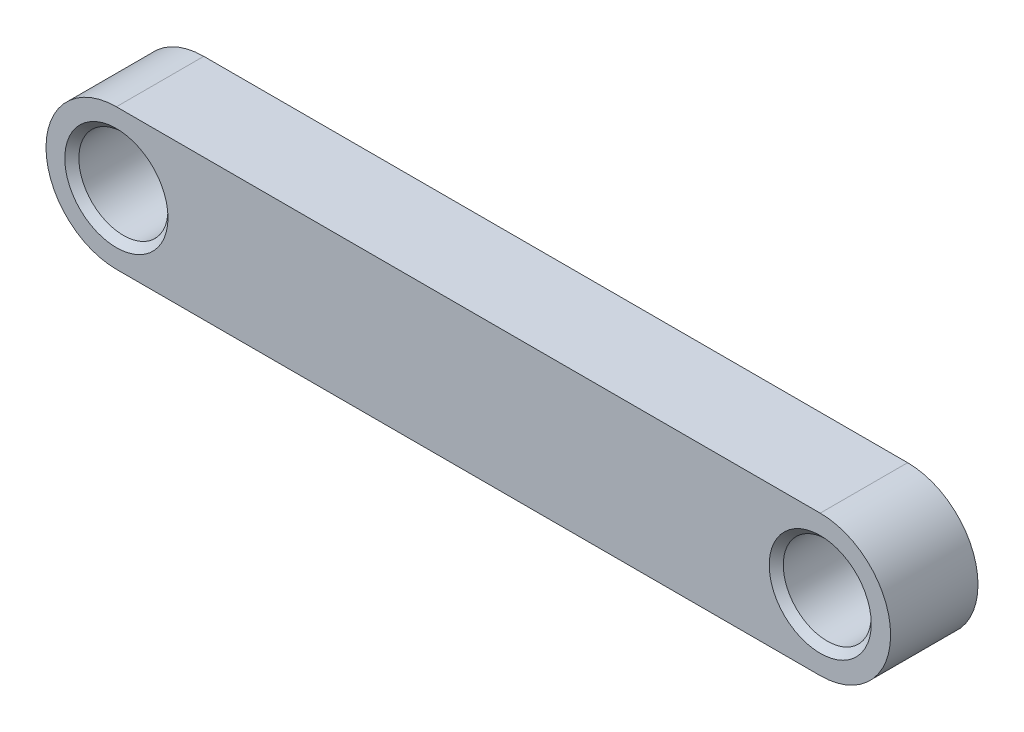
SolidWorks part; units mm, degrees
material "6061-T6 (SS)"
ref_plane "Front Plane" through (0, 0, 0) normal (0, 0, 1) x (1, 0, 0)
ref_plane "Top Plane" through (0, 0, 0) normal (0, 1, 0) x (1, 0, 0)
ref_plane "Right Plane" through (0, 0, 0) normal (1, 0, 0) x (0, 0, -1)
sketch "Sketch1" plane through (0, 0, 0) normal (0, 0, 1) x (1, 0, 0)
  line L0 (-38.1, 0) -> (38.1, 0) construction
  line L1 (-38.1, 7.62) -> (38.1, 7.62)
  line L2 (-38.1, -7.62) -> (38.1, -7.62)
  arc A0 (-38.1, 7.62) -> (-38.1, -7.62) centre (-38.1, 0) ccw
  arc A1 (38.1, -7.62) -> (38.1, 7.62) centre (38.1, 0) ccw
  point P2 (0, 0)
  dimension "D1" = 76.2
  dimension "D2" = 15.24
extrude "Boss-Extrude1" add sketch "Sketch1" along normal blind 9.4615
sketch "Sketch2" plane through (0, 0, 9.4615) normal (0, 0, 1) x (1, 0, 0)
  circle A0 centre (38.1, 0) radius 4.7625
  circle A1 centre (-38.1, 0) radius 4.826
  arc A2 (-38.1, 7.62) -> (-38.1, -7.62) centre (-38.1, 0) ccw construction
  arc A3 (38.1, -7.62) -> (38.1, 7.62) centre (38.1, 0) ccw construction
  dimension "D1" = 9.652
  dimension "D2" = 9.525
extrude "Cut-Extrude1" cut sketch "Sketch2" against normal through all
chamfer "Chamfer1" distance 0.762 angle 45 4 edges at (42.8625, 0, 9.4615) (-33.274, 0, 9.4615) (-33.274, 0, 0) (42.8625, 0, 0)
